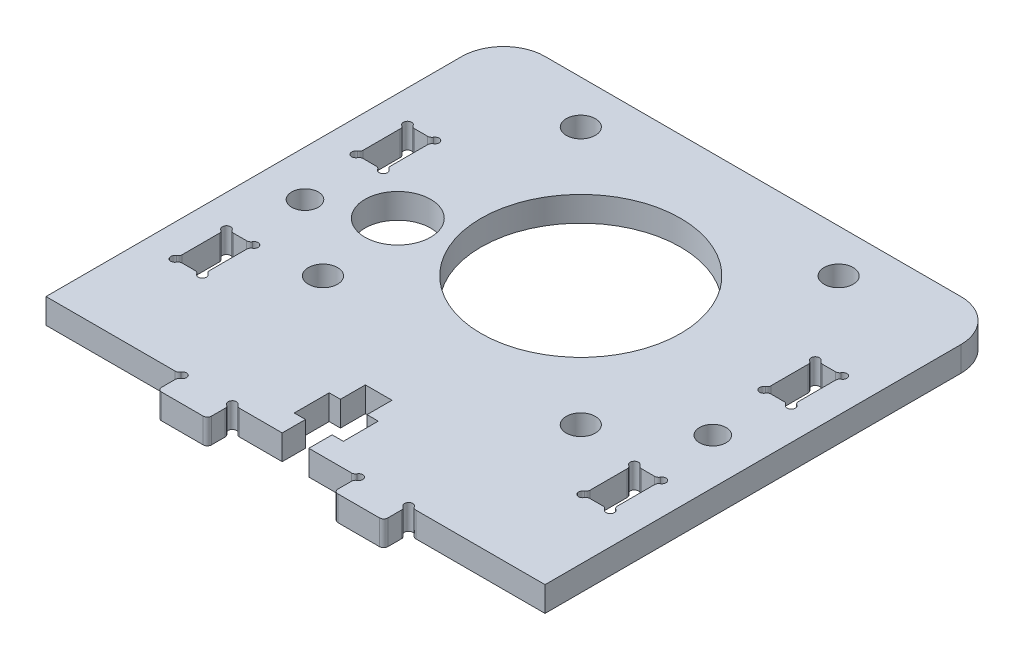
SolidWorks part; units mm, degrees
material "Plain Carbon Steel"
ref_plane "Front Plane" through (0, 0, 0) normal (0, 0, 1) x (1, 0, 0)
ref_plane "Top Plane" through (0, 0, 0) normal (0, 1, 0) x (1, 0, 0)
ref_plane "Right Plane" through (0, 0, 0) normal (1, 0, 0) x (0, 0, -1)
sketch "Sketch1" plane through (0, 0, 0) normal (0, 1, 0) x (1, 0, 0)
  line L0 (365.2434, 1060.953) -> (365.2434, 1056.485)
  line L1 (367.6773, 1061.819) -> (366.1094, 1061.819)
  line L2 (318.6373, 1061.819) -> (317.0694, 1061.819)
  line L3 (312.3734, 1022.1903) -> (327.9073, 1022.1903)
  line L4 (312.3734, 1072.1903) -> (312.3734, 1022.1903)
  line L5 (316.2034, 1039.1936) -> (316.2034, 1034.7256)
  line L6 (318.6373, 1040.0596) -> (317.0694, 1040.0596)
  line L7 (368.5433, 1034.7256) -> (368.5433, 1039.1936)
  line L8 (366.1094, 1033.8596) -> (367.6773, 1033.8596)
  line L9 (365.2434, 1039.1936) -> (365.2434, 1034.7256)
  line L10 (367.6773, 1040.0596) -> (366.1094, 1040.0596)
  line L11 (319.5033, 1056.485) -> (319.5033, 1060.953)
  line L12 (317.0694, 1055.619) -> (318.6373, 1055.619)
  line L13 (316.2034, 1060.953) -> (316.2034, 1056.485)
  line L14 (319.5033, 1034.7256) -> (319.5033, 1039.1936)
  line L15 (317.0694, 1033.8596) -> (318.6373, 1033.8596)
  line L16 (366.1094, 1055.619) -> (367.6773, 1055.619)
  line L17 (343.9733, 1022.1903) -> (349.1073, 1022.1903)
  line L18 (343.9733, 1024.9903) -> (343.9733, 1022.1903)
  line L19 (345.3233, 1024.9903) -> (343.9733, 1024.9903)
  line L20 (345.3233, 1029.1903) -> (345.3233, 1024.9903)
  line L21 (343.9733, 1029.1903) -> (345.3233, 1029.1903)
  line L22 (343.9733, 1032.1903) -> (343.9733, 1029.1903)
  line L23 (367.3733, 1077.1903) -> (317.3733, 1077.1903)
  line L24 (372.3733, 1022.1903) -> (372.3733, 1072.1903)
  line L25 (356.8394, 1022.1903) -> (372.3733, 1022.1903)
  line L26 (355.9733, 1019.6902) -> (355.9733, 1021.3243)
  line L27 (350.4733, 1019.1902) -> (355.4733, 1019.1902)
  line L28 (349.9733, 1021.3243) -> (349.9733, 1019.6902)
  line L29 (340.7733, 1032.1903) -> (343.9733, 1032.1903)
  line L30 (340.7733, 1029.1903) -> (340.7733, 1032.1903)
  line L31 (339.4233, 1029.1903) -> (340.7733, 1029.1903)
  line L32 (339.4233, 1024.9903) -> (339.4233, 1029.1903)
  line L33 (340.7733, 1024.9903) -> (339.4233, 1024.9903)
  line L34 (340.7733, 1022.1903) -> (340.7733, 1024.9903)
  line L35 (335.6394, 1022.1903) -> (340.7733, 1022.1903)
  line L36 (368.5433, 1056.485) -> (368.5433, 1060.953)
  line L37 (334.7733, 1019.6902) -> (334.7733, 1021.3243)
  line L38 (329.2733, 1019.1902) -> (334.2733, 1019.1902)
  line L39 (328.7733, 1021.3243) -> (328.7733, 1019.6902)
  line L40 (372.3733, 1022.1903) -> (312.3734, 1022.1903) construction
  line L41 (317.8533, 1047.1903) -> (317.8533, 1081.5508) construction
  line L42 (368.0078, 1047.1903) -> (368.0078, 1096.6784) construction
  line L43 (372.3733, 1047.8425) -> (312.3734, 1047.8425) construction
  line L44 (372.3733, 1047.1903) -> (312.3734, 1047.1903) construction
  line L45 (380.2472, 1037.1058) -> (356.8394, 1037.1058) construction
  line L46 (380.2472, 1058.9023) -> (356.8394, 1058.9023) construction
  line L47 (307.0334, 1058.9093) -> (325.3733, 1058.9093) construction
  line L48 (330.3637, 1037.1128) -> (308.6429, 1037.1128) construction
  line L49 (330.3637, 1051.8885) -> (308.6429, 1051.8885) construction
  line L50 (372.3733, 1036.9659) -> (312.3734, 1036.9659) construction
  line L51 (372.3733, 1058.719) -> (312.3734, 1058.719) construction
  arc A0 (317.3733, 1077.1903) -> (312.3734, 1072.1903) centre (317.3733, 1072.1903) ccw
  arc A1 (364.9934, 1056.052) -> (365.6764, 1055.369) centre (365.2434, 1055.619) ccw
  arc A2 (364.9934, 1056.052) -> (365.2434, 1056.485) centre (364.7434, 1056.485) ccw
  arc A3 (365.6764, 1062.069) -> (366.1094, 1061.819) centre (366.1094, 1062.319) ccw
  arc A4 (316.6364, 1062.069) -> (317.0694, 1061.819) centre (317.0694, 1062.319) ccw
  arc A5 (365.2434, 1060.953) -> (364.9934, 1061.386) centre (364.7434, 1060.953) ccw
  arc A6 (365.6764, 1062.069) -> (364.9934, 1061.386) centre (365.2434, 1061.819) ccw
  arc A7 (366.1094, 1055.619) -> (365.6764, 1055.369) centre (366.1094, 1055.119) ccw
  arc A8 (315.9534, 1034.2926) -> (316.2034, 1034.7256) centre (315.7034, 1034.7256) ccw
  arc A9 (316.2034, 1039.1936) -> (315.9534, 1039.6266) centre (315.7034, 1039.1936) ccw
  arc A10 (316.6364, 1040.3096) -> (315.9534, 1039.6266) centre (316.2034, 1040.0596) ccw
  arc A11 (316.6364, 1040.3096) -> (317.0694, 1040.0596) centre (317.0694, 1040.5596) ccw
  arc A12 (367.6773, 1061.819) -> (368.1103, 1062.069) centre (367.6773, 1062.319) ccw
  arc A13 (368.7933, 1039.6266) -> (368.1103, 1040.3096) centre (368.5433, 1040.0596) ccw
  arc A14 (368.7933, 1039.6266) -> (368.5433, 1039.1936) centre (369.0433, 1039.1936) ccw
  arc A15 (368.5433, 1034.7256) -> (368.7933, 1034.2926) centre (369.0433, 1034.7256) ccw
  arc A16 (368.1103, 1033.6096) -> (368.7933, 1034.2926) centre (368.5433, 1033.8596) ccw
  arc A17 (368.1103, 1033.6096) -> (367.6773, 1033.8596) centre (367.6773, 1033.3596) ccw
  arc A18 (366.1094, 1033.8596) -> (365.6764, 1033.6096) centre (366.1094, 1033.3596) ccw
  arc A19 (364.9934, 1034.2926) -> (365.6764, 1033.6096) centre (365.2434, 1033.8596) ccw
  arc A20 (364.9934, 1034.2926) -> (365.2434, 1034.7256) centre (364.7434, 1034.7256) ccw
  arc A21 (365.2434, 1039.1936) -> (364.9934, 1039.6266) centre (364.7434, 1039.1936) ccw
  arc A22 (365.6764, 1040.3096) -> (364.9934, 1039.6266) centre (365.2434, 1040.0596) ccw
  arc A23 (365.6764, 1040.3096) -> (366.1094, 1040.0596) centre (366.1094, 1040.5596) ccw
  arc A24 (367.6773, 1040.0596) -> (368.1103, 1040.3096) centre (367.6773, 1040.5596) ccw
  arc A25 (319.7533, 1061.386) -> (319.0703, 1062.069) centre (319.5033, 1061.819) ccw
  arc A26 (319.7533, 1061.386) -> (319.5033, 1060.953) centre (320.0033, 1060.953) ccw
  arc A27 (319.5033, 1056.485) -> (319.7533, 1056.052) centre (320.0033, 1056.485) ccw
  arc A28 (319.0703, 1055.369) -> (319.7533, 1056.052) centre (319.5033, 1055.619) ccw
  arc A29 (319.0703, 1055.369) -> (318.6373, 1055.619) centre (318.6373, 1055.119) ccw
  arc A30 (317.0694, 1055.619) -> (316.6364, 1055.369) centre (317.0694, 1055.119) ccw
  arc A31 (315.9534, 1056.052) -> (316.6364, 1055.369) centre (316.2034, 1055.619) ccw
  arc A32 (315.9534, 1056.052) -> (316.2034, 1056.485) centre (315.7034, 1056.485) ccw
  arc A33 (316.2034, 1060.953) -> (315.9534, 1061.386) centre (315.7034, 1060.953) ccw
  arc A34 (316.6364, 1062.069) -> (315.9534, 1061.386) centre (316.2034, 1061.819) ccw
  circle A35 centre (366.8933, 1047.8425) radius 1.6
  circle A36 centre (357.8733, 1071.9903) radius 1.75
  circle A37 centre (357.8733, 1040.9903) radius 1.75
  arc A38 (318.6373, 1061.819) -> (319.0703, 1062.069) centre (318.6373, 1062.319) ccw
  arc A39 (319.7533, 1039.6266) -> (319.0703, 1040.3096) centre (319.5033, 1040.0596) ccw
  arc A40 (319.7533, 1039.6266) -> (319.5033, 1039.1936) centre (320.0033, 1039.1936) ccw
  arc A41 (319.5033, 1034.7256) -> (319.7533, 1034.2926) centre (320.0033, 1034.7256) ccw
  arc A42 (319.0703, 1033.6096) -> (319.7533, 1034.2926) centre (319.5033, 1033.8596) ccw
  arc A43 (319.0703, 1033.6096) -> (318.6373, 1033.8596) centre (318.6373, 1033.3596) ccw
  arc A44 (315.9534, 1034.2926) -> (316.6364, 1033.6096) centre (316.2034, 1033.8596) ccw
  arc A45 (349.1073, 1022.1903) -> (349.5403, 1022.4403) centre (349.1073, 1022.6903) ccw
  arc A46 (318.6373, 1040.0596) -> (319.0703, 1040.3096) centre (318.6373, 1040.5596) ccw
  circle A47 centre (325.3733, 1051.4903) radius 3.95
  circle A48 centre (342.3733, 1056.4903) radius 12
  arc A49 (372.3733, 1072.1903) -> (367.3733, 1077.1903) centre (367.3733, 1072.1903) ccw
  arc A50 (356.4064, 1022.4403) -> (356.8394, 1022.1903) centre (356.8394, 1022.6903) ccw
  arc A51 (356.4064, 1022.4403) -> (355.7233, 1021.7573) centre (355.9733, 1022.1903) ccw
  arc A52 (355.9733, 1021.3243) -> (355.7233, 1021.7573) centre (355.4733, 1021.3243) ccw
  arc A53 (355.4733, 1019.1902) -> (355.9733, 1019.6902) centre (355.4733, 1019.6902) ccw
  arc A54 (349.9733, 1019.6902) -> (350.4733, 1019.1902) centre (350.4733, 1019.6902) ccw
  arc A55 (350.2233, 1021.7573) -> (349.9733, 1021.3243) centre (350.4733, 1021.3243) ccw
  arc A56 (350.2233, 1021.7573) -> (349.5403, 1022.4403) centre (349.9733, 1022.1903) ccw
  arc A57 (317.0694, 1033.8596) -> (316.6364, 1033.6096) centre (317.0694, 1033.3596) ccw
  arc A58 (327.9073, 1022.1903) -> (328.3403, 1022.4403) centre (327.9073, 1022.6903) ccw
  arc A59 (335.2063, 1022.4403) -> (335.6394, 1022.1903) centre (335.6394, 1022.6903) ccw
  circle A60 centre (326.8733, 1071.9903) radius 1.75
  circle A61 centre (326.8733, 1040.9903) radius 1.75
  circle A62 centre (317.8533, 1047.8495) radius 1.6
  arc A63 (368.7933, 1061.386) -> (368.1103, 1062.069) centre (368.5433, 1061.819) ccw
  arc A64 (368.5433, 1056.485) -> (368.7933, 1056.052) centre (369.0433, 1056.485) ccw
  arc A65 (335.2063, 1022.4403) -> (334.5233, 1021.7573) centre (334.7733, 1022.1903) ccw
  arc A66 (334.7733, 1021.3243) -> (334.5233, 1021.7573) centre (334.2733, 1021.3243) ccw
  arc A67 (368.7933, 1061.386) -> (368.5433, 1060.953) centre (369.0433, 1060.953) ccw
  arc A68 (328.7733, 1019.6902) -> (329.2733, 1019.1902) centre (329.2733, 1019.6902) ccw
  arc A69 (368.1103, 1055.369) -> (368.7933, 1056.052) centre (368.5433, 1055.619) ccw
  arc A70 (368.1103, 1055.369) -> (367.6773, 1055.619) centre (367.6773, 1055.119) ccw
  arc A71 (329.0233, 1021.7573) -> (328.3403, 1022.4403) centre (328.7733, 1022.1903) ccw
  arc A72 (334.2733, 1019.1902) -> (334.7733, 1019.6902) centre (334.2733, 1019.6902) ccw
  arc A73 (329.0233, 1021.7573) -> (328.7733, 1021.3243) centre (329.2733, 1021.3243) ccw
  point P193 (317.8533, 1047.8495)
  point P202 (368.5433, 1036.9596)
  point P205 (368.5433, 1058.719)
  point P208 (316.2034, 1058.719)
  point P211 (319.5033, 1036.9596)
  dimension "D3" = 14.7757
  dimension "D1" = 25
  dimension "D2" = 25.6522
  dimension "D4" = 36.5287
extrude "Boss-Extrude1" add sketch "Sketch1" along normal blind 3
